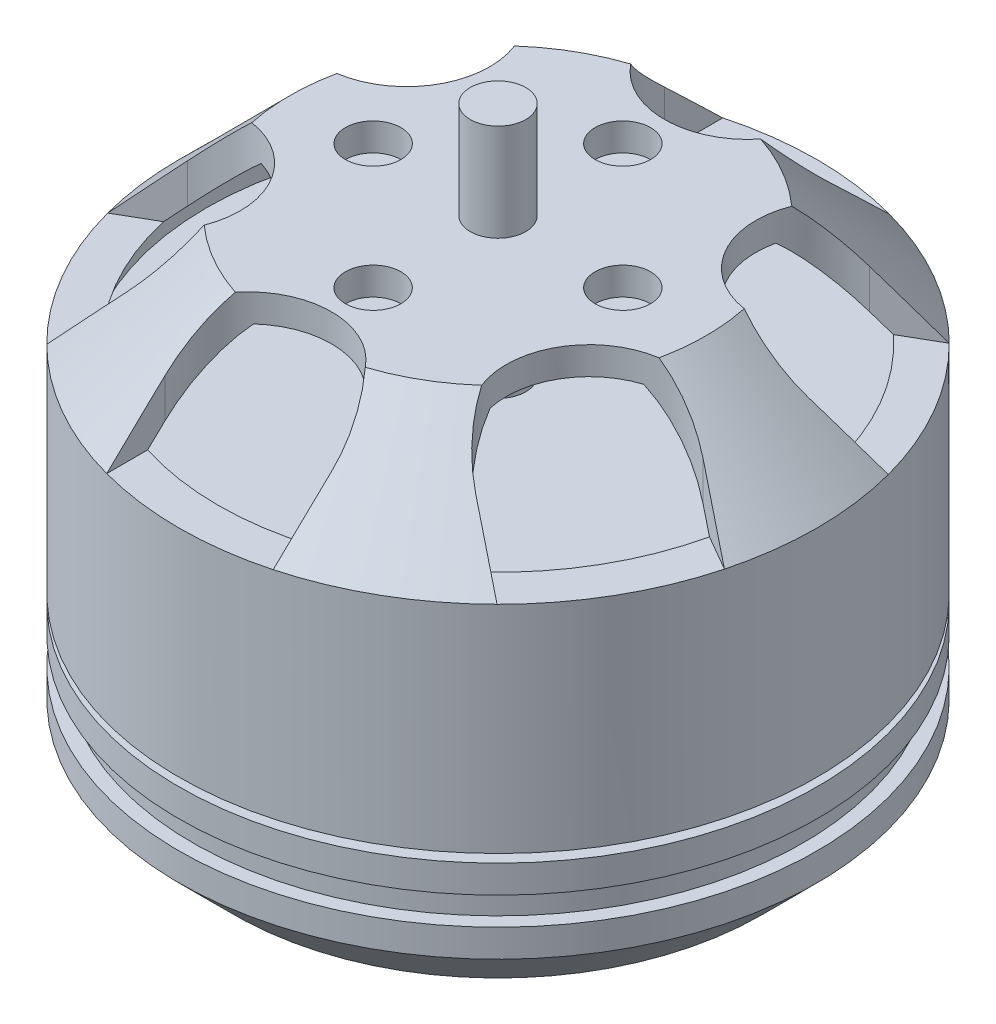
SolidWorks part; units mm, degrees
ref_plane "Front Plane" through (0, 0, 0) normal (0, 0, 1) x (1, 0, 0)
ref_plane "Top Plane" through (0, 0, 0) normal (0, 1, 0) x (1, 0, 0)
ref_plane "Right Plane" through (0, 0, 0) normal (1, 0, 0) x (0, 0, -1)
sketch "Sketch2" plane through (0, 0, 0) normal (0, 0, 1) x (1, 0, 0)
  line L0 (0, 0) -> (-1, 0)
  line L1 (-1, 0) -> (-1, -22.38)
  line L2 (-1, -22.38) -> (0, -22.38)
  line L3 (0, -22.38) -> (0, -20.58)
  line L4 (0, -20.58) -> (8.5, -20.58)
  line L5 (8.5, -20.58) -> (10.5, -18.58)
  line L6 (0, 0) -> (0, -3.5)
  line L7 (0, -3.5) -> (6.5, -3.5)
  line L8 (6.5, -3.5) -> (10.5, -7.5)
  line L9 (10.5, -18.58) -> (10.5, -17.58)
  line L10 (10.5, -17.58) -> (10, -17.58)
  line L11 (10, -17.58) -> (10, -16.58)
  line L12 (10, -16.58) -> (10.5, -16.58)
  line L13 (10.5, -16.58) -> (10.5, -15.58)
  line L14 (10.5, -15.58) -> (8.5, -15.58)
  line L15 (8.5, -15.58) -> (8.5, -15.28)
  line L16 (8.5, -15.28) -> (10.5, -15.28)
  line L17 (10.5, -7.5) -> (10.5, -15.28)
  line L18 (1, -4.5) -> (6.0858, -4.5)
  line L19 (6.0858, -4.5) -> (9.5, -7.9142)
  line L20 (0, -4.5) -> (6.0858, -4.5) construction
  line L21 (9.5, -8.5) -> (9.5, -7.9142)
  line L22 (6.0858, -4.5) -> (9.7929, -8.2071) construction
  line L23 (9.5, -8.5) -> (0, -8.5)
  line L24 (0, -8.5) -> (0, -5.5)
  line L25 (0, -5.5) -> (1, -5.5)
  line L26 (1, -5.5) -> (1, -4.5)
  point P3 (10.5, -7.5)
  point P25 (0, 0)
  point P26 (9.5, -8.5)
  dimension "D1" = 1
  dimension "D2" = 22.38
  dimension "D3" = 1
  dimension "D4" = 1.8
  dimension "D5" = 8.5
  dimension "D6" = 2
  dimension "D7" = 2
  dimension "D8" = 3.5
  dimension "D9" = 6.5
  dimension "D10" = 4
  dimension "D11" = 4
  dimension "D12" = 1
  dimension "D13" = 0.5
  dimension "D14" = 1
  dimension "D15" = 0.5
  dimension "D16" = 1
  dimension "D17" = 2
  dimension "D18" = 0.3
  dimension "D20" = 1
  dimension "D21" = 1
  dimension "D22" = 1
  dimension "D23" = 1
  dimension "D19" = 1
revolve "Revolve1" add sketch "Sketch2" angle 360 about L1
sketch "Sketch4" plane through (0, -20.58, 0) normal (0, -1, 0) x (1, 0, 0)
  circle A0 centre (-1, 0) radius 5 construction
  circle A1 centre (-1, 5) radius 1.1
  circle A2 centre (4, 0) radius 1.1
  circle A3 centre (-1, -5) radius 1.1
  circle A4 centre (-6, 0) radius 1.1
  point P14 (-1, 0)
  dimension "D1" = 10
  dimension "D2" = 2.2
  dimension "D3" = 4
extrude "Cut-Extrude1" cut sketch "Sketch4" against normal blind 3.5
sketch "Sketch5" plane through (0, -3.5, 0) normal (0, 1, 0) x (1, 0, 0)
  line L0 (2, 9) -> (2, 12)
  line L1 (2, 12) -> (-4, 12)
  line L2 (-4, 9) -> (-4, 12)
  line L3 (8.2942, 1.9019) -> (10.8923, 3.4019)
  line L4 (10.8923, 3.4019) -> (7.8923, 8.5981)
  line L5 (5.2942, 7.0981) -> (7.8923, 8.5981)
  line L6 (5.2942, -7.0981) -> (7.8923, -8.5981)
  line L7 (7.8923, -8.5981) -> (10.8923, -3.4019)
  line L8 (8.2942, -1.9019) -> (10.8923, -3.4019)
  line L9 (-4, -9) -> (-4, -12)
  line L10 (-4, -12) -> (2, -12)
  line L11 (2, -9) -> (2, -12)
  line L12 (-10.2942, -1.9019) -> (-12.8923, -3.4019)
  line L13 (-12.8923, -3.4019) -> (-9.8923, -8.5981)
  line L14 (-7.2942, -7.0981) -> (-9.8923, -8.5981)
  line L15 (-7.2942, 7.0981) -> (-9.8923, 8.5981)
  line L16 (-9.8923, 8.5981) -> (-12.8923, 3.4019)
  line L17 (-10.2942, 1.9019) -> (-12.8923, 3.4019)
  circle A0 centre (-1, 0) radius 4.5 construction
  circle A1 centre (-1, 4.5) radius 1
  circle A2 centre (3.5, 0) radius 1
  circle A3 centre (-1, -4.5) radius 1
  circle A4 centre (-5.5, 0) radius 1
  circle A5 centre (-1, 0) radius 9 construction
  arc A6 (-4, 9) -> (2, 9) centre (-1, 9) ccw
  arc A7 (5.2942, 7.0981) -> (8.2942, 1.9019) centre (6.7942, 4.5) ccw
  arc A8 (8.2942, -1.9019) -> (5.2942, -7.0981) centre (6.7942, -4.5) ccw
  arc A9 (2, -9) -> (-4, -9) centre (-1, -9) ccw
  arc A10 (-7.2942, -7.0981) -> (-10.2942, -1.9019) centre (-8.7942, -4.5) ccw
  arc A11 (-10.2942, 1.9019) -> (-7.2942, 7.0981) centre (-8.7942, 4.5) ccw
  point P14 (-1, 0)
  point P45 (-1, 0)
  dimension "D1" = 9
  dimension "D2" = 2
  dimension "D4" = 18
  dimension "D5" = 6
  dimension "D6" = 6
  dimension "D3" = 4
extrude "Cut-Extrude2" cut sketch "Sketch5" against normal blind 4
